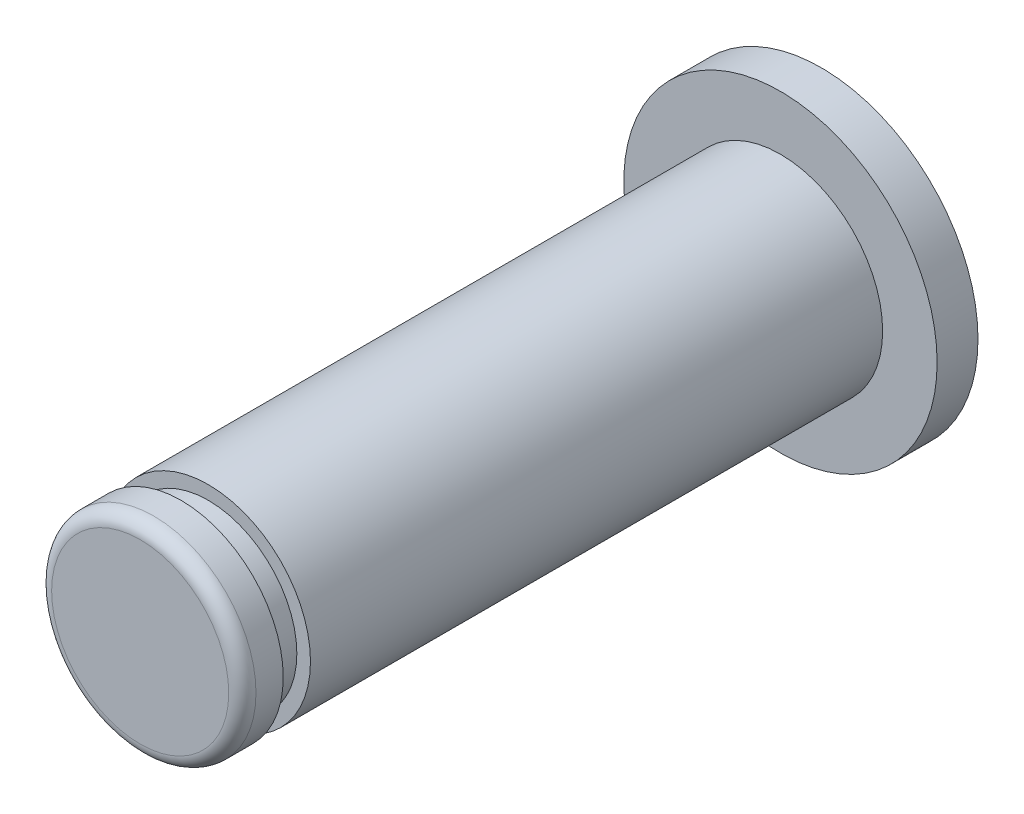
SolidWorks part; units mm, degrees
ref_plane "Plan de face" through (0, 0, 0) normal (0, 0, 1) x (1, 0, 0)
ref_plane "Plan de dessus" through (0, 0, 0) normal (0, 1, 0) x (1, 0, 0)
ref_plane "Plan de droite" through (0, 0, 0) normal (1, 0, 0) x (0, 0, -1)
sketch "Esquisse1" plane through (0, 0, 0) normal (0, 0, 1) x (1, 0, 0)
  circle A0 centre (0, 0) radius 7.5
  dimension "D1" = 15
extrude "Boss.-Extru.1" add sketch "Esquisse1" along normal blind 45 contours A0
sketch "Esquisse2" plane through (0, 0, 0) normal (0, 0, 1) x (1, 0, 0)
  circle A0 centre (0, 0) radius 11.5
  dimension "D1" = 23
extrude "Boss.-Extru.2" add sketch "Esquisse2" along normal blind 3
sketch "Esquisse3" plane through (0, 0, 0) normal (0, 0, 1) x (1, 0, 0)
  circle A0 centre (0, 0) radius 6.5
  dimension "D1" = 13
extrude "Boss.-Extru.3" add sketch "Esquisse3" along normal blind 2 from offset 45
sketch "Esquisse4" plane through (0, 0, 0) normal (0, 0, 1) x (1, 0, 0)
  circle A0 centre (0, 0) radius 7.5
  dimension "D1" = 15
extrude "Boss.-Extru.4" add sketch "Esquisse4" along normal blind 3 from offset 47
fillet "Congé1" radius 1 1 edges at (7.5, 0, 50)
